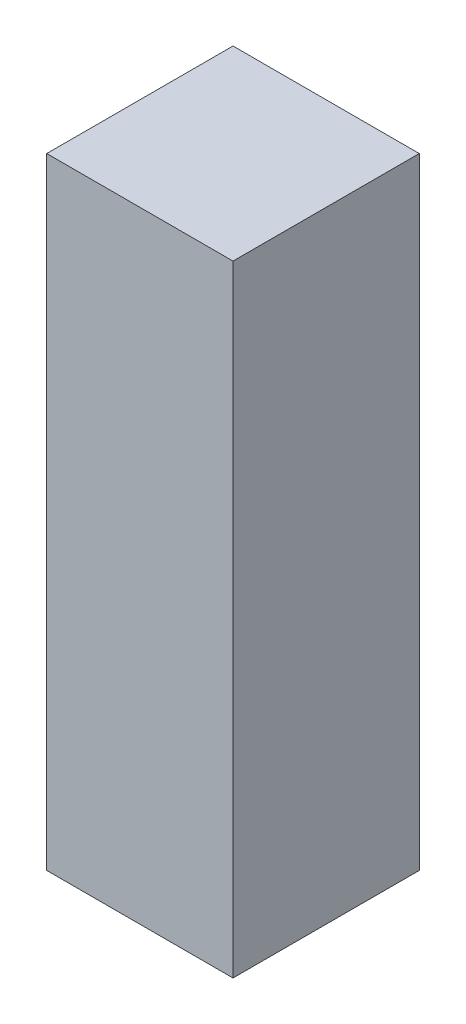
SolidWorks part; units mm, degrees
ref_plane "Front Plane" through (0, 0, 0) normal (0, 0, 1) x (1, 0, 0)
ref_plane "Top Plane" through (0, 0, 0) normal (0, 1, 0) x (1, 0, 0)
ref_plane "Right Plane" through (0, 0, 0) normal (1, 0, 0) x (0, 0, -1)
sketch "Sketch3" plane through (0, 0, 0) normal (0, 0, 1) x (1, 0, 0)
  line L1 (-15, -50) -> (15, -50)
  line L2 (-15, -50) -> (-15, 50)
  line L3 (-15, 50) -> (15, 50)
  line L4 (15, -50) -> (15, 50)
  line L5 (-15, -50) -> (15, 50) construction
  line L6 (-15, 50) -> (15, -50) construction
  point P0 (0, 0)
  dimension "D1" = 30
  dimension "D2" = 100
extrude "Boss-Extrude1" add sketch "Sketch3" along normal mid plane 30
